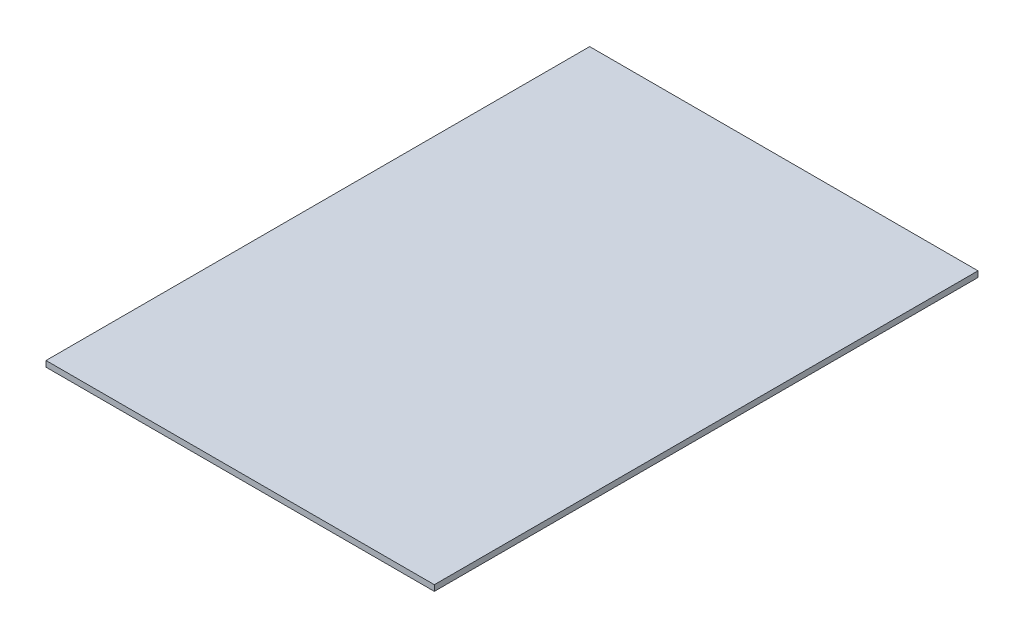
SolidWorks part; units mm, degrees
ref_plane "Face" through (0, 0, 0) normal (0, 0, 1) x (1, 0, 0)
ref_plane "Dessus" through (0, 0, 0) normal (0, 1, 0) x (1, 0, 0)
ref_plane "Droite" through (0, 0, 0) normal (1, 0, 0) x (0, 0, -1)
sketch "Esquisse1" plane through (0, 0, 0) normal (0, 1, 0) x (1, 0, 0)
  line L0 (0, 140) -> (100, 140) construction
  line L1 (0, 0) -> (200, 0)
  line L2 (0, 0) -> (0, 280)
  line L3 (0, 280) -> (200, 280)
  line L4 (200, 0) -> (200, 280)
  line L5 (100, 140) -> (200, 140) construction
  line L6 (0, 0) -> (100, 140) construction
  line L7 (100, 140) -> (200, 0) construction
  line L8 (0, 280) -> (100, 140) construction
  line L9 (100, 140) -> (200, 280) construction
  line L10 (50, 280) -> (50, 0) construction
  line L11 (100, 280) -> (100, 140) construction
  line L12 (100, 140) -> (100, 0) construction
  line L13 (0, 210) -> (200, 210) construction
  line L14 (150, 280) -> (150, 0) construction
  line L15 (0, 70) -> (200, 70) construction
  point P8 (50, 140)
  point P13 (150, 140)
  point P14 (100, 210)
  point P15 (100, 70)
  dimension "D1" = 200
  dimension "D2" = 280
extrude "Extrusion1" add sketch "Esquisse1" along normal blind 3
